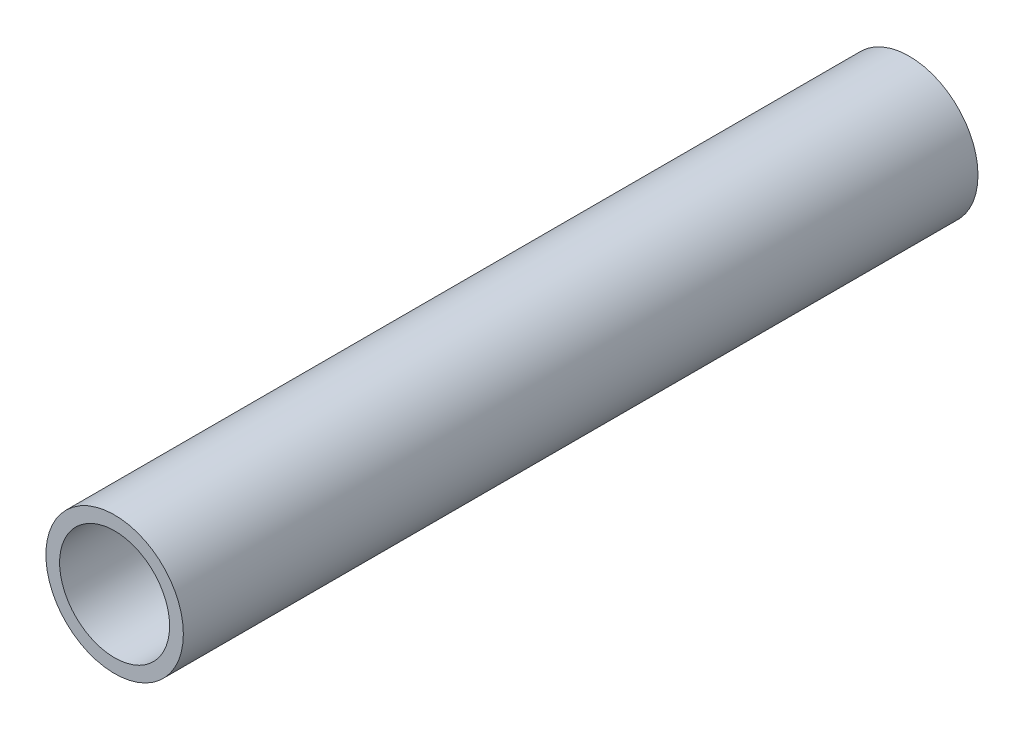
SolidWorks part; units mm, degrees
ref_plane "Front Plane" through (0, 0, 0) normal (0, 0, 1) x (1, 0, 0)
ref_plane "Top Plane" through (0, 0, 0) normal (0, 1, 0) x (1, 0, 0)
ref_plane "Right Plane" through (0, 0, 0) normal (1, 0, 0) x (0, 0, -1)
sketch "Sketch1" plane through (0, 0, 0) normal (0, 0, 1) x (1, 0, 0)
  circle A0 centre (0, 0) radius 1.25
  circle A1 centre (0, 0) radius 1
extrude "Boss-Extrude1" add sketch "Sketch1" along normal blind 14.45
equation "\"D1@Boss-Extrude1\"= \"HL@parametersSketch@prostheticParameters.SLDPRT\" * 0.17 - 4 - 3 - 10 'Middle Tube"
